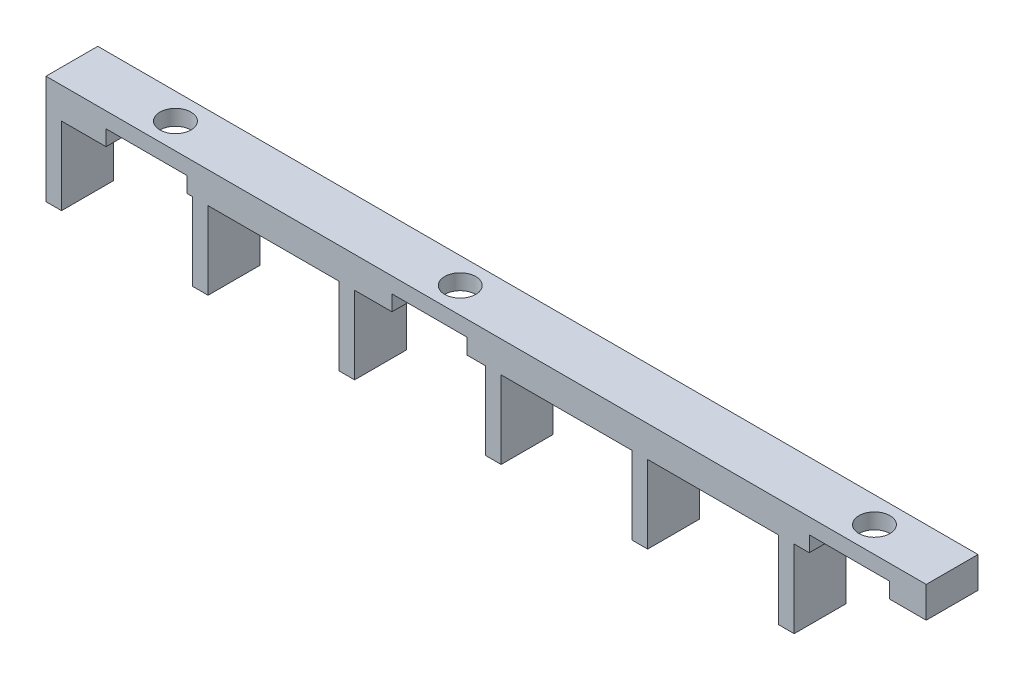
SolidWorks part; units mm, degrees
ref_plane "Front Plane" through (0, 0, 0) normal (0, 0, 1) x (1, 0, 0)
ref_plane "Top Plane" through (0, 0, 0) normal (0, 1, 0) x (1, 0, 0)
ref_plane "Right Plane" through (0, 0, 0) normal (1, 0, 0) x (0, 0, -1)
sketch "Sketch1" plane through (0, 0, 0) normal (0, 1, 0) x (1, 0, 0)
  line L1 (-300, 5) -> (-130, 5)
  line L2 (-300, 5) -> (-300, -5)
  line L3 (-300, -5) -> (-130, -5)
  line L4 (-130, 5) -> (-130, -5)
  point P4 (0, 0)
  point P5 (0, 0)
  point P6 (0, 0)
  point P7 (0, 0)
  point P8 (0, 0)
extrude "Boss-Extrude1" add sketch "Sketch1" along normal blind 6
sketch "Sketch3" plane through (0, 0, 0) normal (0, -1, 0) x (1, 0, 0)
  line L2 (-300, -5) -> (-297, -5)
  line L3 (-300, -5) -> (-300, 5)
  line L4 (-300, 5) -> (-297, 5)
  line L5 (-297, -5) -> (-297, 5)
  point P4 (0, 0)
  point P5 (0, 0)
  point P6 (0, 0)
  point P9 (0, 0)
  point P10 (0, 0)
  point P11 (0, 0)
extrude "Boss-Extrude2" add sketch "Sketch3" along normal blind 15
pattern_linear "LPattern1" count 6 spacing 28.3 along (1, 0, 0) of "Boss-Extrude2"
sketch "Sketch5" plane through (0, 6, 0) normal (0, 1, 0) x (1, 0, 0)
  line L0 (-300, 5) -> (-300, -5) construction
  line L1 (-300, -5) -> (-300, 5) construction
  circle A0 centre (-225, 0) radius 3
  circle A3 centre (225, 0) radius 1.8
  circle A4 centre (165, 0) radius 1.8
  circle A5 centre (-280, 0) radius 3
  circle A6 centre (-145, 0) radius 3
  point P14 (0, 0)
  point P15 (0, 0)
  dimension "D1" = 20
  dimension "D2" = 75
  dimension "D3" = 155
extrude "Cut-Extrude1" cut sketch "Sketch5" against normal blind 10
sketch "Sketch7" plane through (0, 0, 0) normal (0, -1, 0) x (1, 0, 0)
  line L1 (-288.4082, 14.7964) -> (-272.7977, 14.7964)
  line L2 (-288.4082, 14.7964) -> (-288.4082, -14.6269)
  line L3 (-288.4082, -14.6269) -> (-272.7977, -14.6269)
  line L4 (-272.7977, 14.7964) -> (-272.7977, -14.6269)
  line L5 (-218.6437, 9.9012) -> (-233.1875, 9.9012)
  line L6 (-218.6437, 9.9012) -> (-218.6437, -10.3605)
  line L7 (-218.6437, -10.3605) -> (-233.1875, -10.3605)
  line L8 (-233.1875, 9.9012) -> (-233.1875, -10.3605)
  line L9 (-137.1248, 13.2777) -> (-152.5878, 13.2777)
  line L10 (-137.1248, 13.2777) -> (-137.1248, -13.5987)
  line L11 (-137.1248, -13.5987) -> (-152.5878, -13.5987)
  line L12 (-152.5878, 13.2777) -> (-152.5878, -13.5987)
extrude "Cut-Extrude3" cut sketch "Sketch7" against normal blind 3
